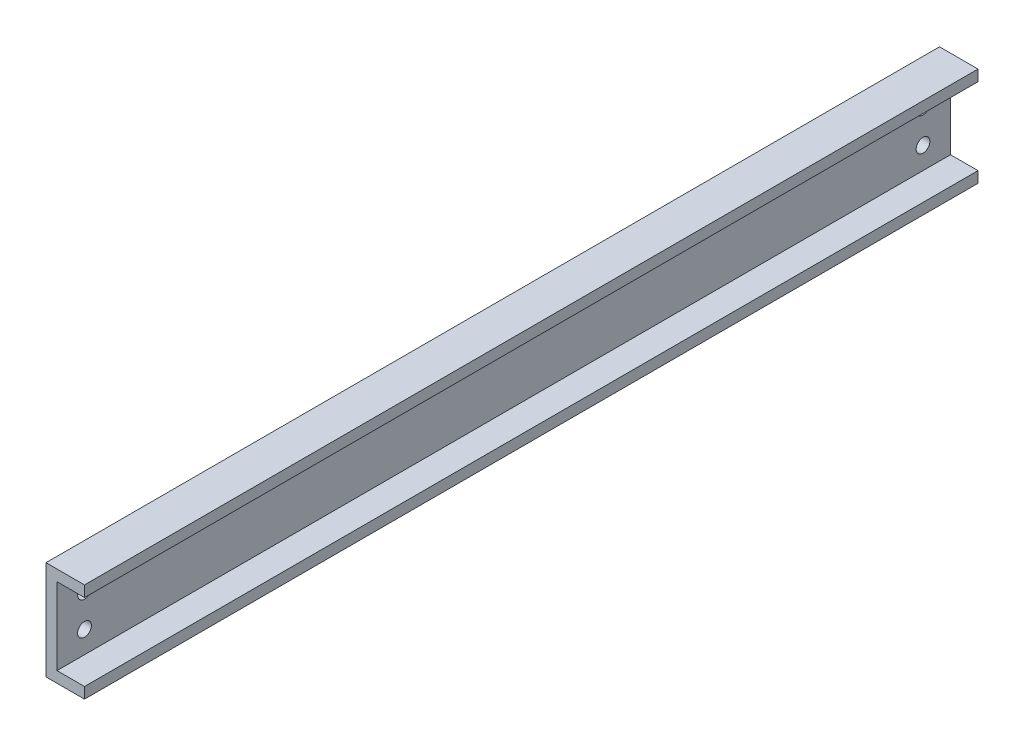
SolidWorks part; units mm, degrees
ref_plane "Front Plane" through (0, 0, 0) normal (0, 0, 1) x (1, 0, 0)
ref_plane "Top Plane" through (0, 0, 0) normal (0, 1, 0) x (1, 0, 0)
ref_plane "Right Plane" through (0, 0, 0) normal (1, 0, 0) x (0, 0, -1)
sketch "Sketch1" plane through (0, 0, 0) normal (0, 0, 1) x (1, 0, 0)
  line L0 (0, 9) -> (0, -9)
  line L1 (0, -9) -> (7, -9)
  line L2 (0, 9) -> (7, 9)
  line L3 (2, -7) -> (7, -7)
  line L4 (2, 7) -> (2, -7)
  line L5 (2, 7) -> (7, 7)
  line L6 (7, -9) -> (7, -7)
  line L7 (7, 9) -> (7, 7)
  dimension "D1" = 18
  dimension "D2" = 9
  dimension "D3" = 7
  dimension "D4" = 7
  dimension "D5" = 2
extrude "Boss-Extrude1" add sketch "Sketch1" against normal blind 162.5
sketch "Sketch2" plane through (0, 0, 0) normal (-1, 0, 0) x (0, 0, 1)
  line L0 (-2, 9) -> (-2, -9) construction
  line L1 (-162.5, 9) -> (0, 9) construction
  line L2 (-162.5, -9) -> (0, -9) construction
  line L3 (0, 9) -> (0, -9) construction
  line L4 (0, 0) -> (-162.5, 0) construction
  line L5 (-162.5, 9) -> (-162.5, -9) construction
  line L6 (-81.25, 9) -> (-81.25, -9) construction
  circle A0 centre (-5, 3) radius 1.25
  circle A2 centre (-5, -3) radius 1.25
  circle A3 centre (-157.5, -3) radius 1.25
  circle A4 centre (-157.5, 3) radius 1.25
  dimension "D2" = 2.5
  dimension "D1" = 2
  dimension "D3" = 3
  dimension "D4" = 3
extrude "Cut-Extrude1" cut sketch "Sketch2" against normal through all
